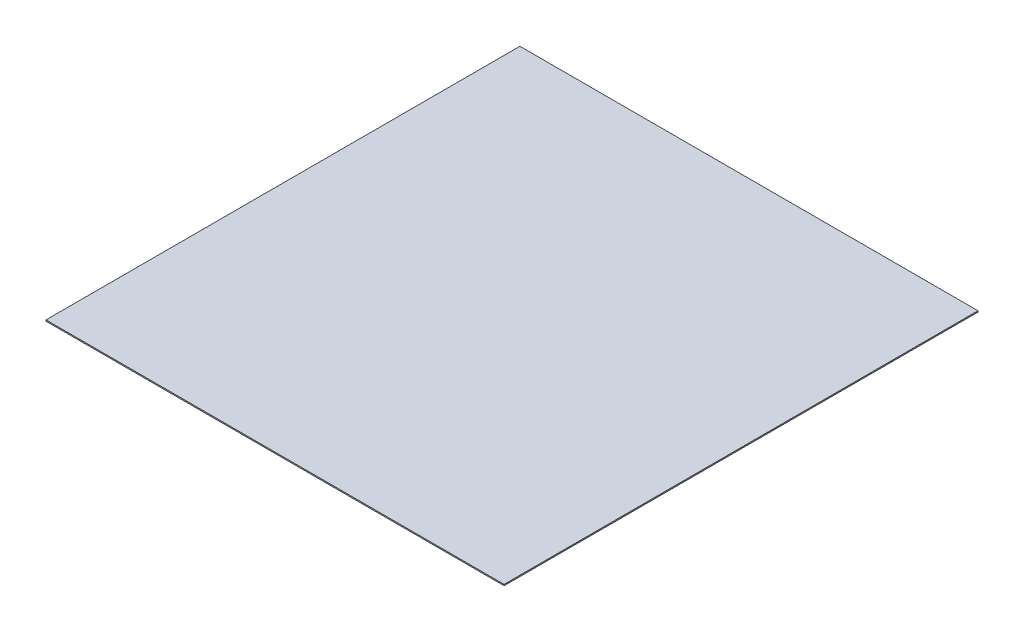
SolidWorks part; units mm, degrees
material "silicon D"
ref_plane "Front" through (0, 0, 0) normal (0, 0, 1) x (1, 0, 0)
ref_plane "Top" through (0, 0, 0) normal (0, 1, 0) x (1, 0, 0)
ref_plane "Right" through (0, 0, 0) normal (1, 0, 0) x (0, 0, -1)
sketch "Sketch1" plane through (0, 0, 0) normal (0, 1, 0) x (1, 0, 0)
  line L0 (-9.6048, -9.936) -> (9.6048, 9.936) construction
  line L1 (-9.6048, 9.936) -> (9.6048, 9.936)
  line L2 (-9.6048, 9.936) -> (-9.6048, -9.936)
  line L3 (-9.6048, -9.936) -> (9.6048, -9.936)
  line L4 (9.6048, 9.936) -> (9.6048, -9.936)
  point P4 (0, 0)
  dimension "D1" = 19.872
  dimension "D2" = 19.2096
extrude "Extrude1" add sketch "Sketch1" along normal blind 0.05
